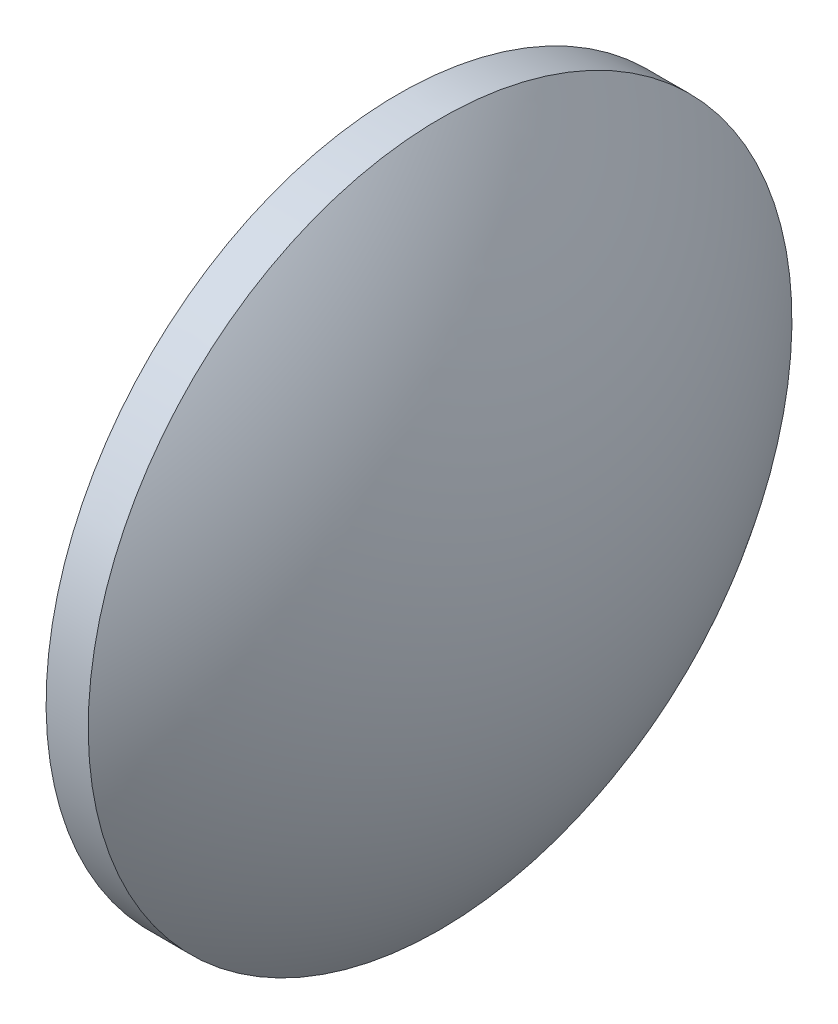
SolidWorks part; units mm, degrees
ref_plane "前视基准面" through (0, 0, 0) normal (0, 0, 1) x (1, 0, 0)
ref_plane "上视基准面" through (0, 0, 0) normal (0, 1, 0) x (1, 0, 0)
ref_plane "右视基准面" through (0, 0, 0) normal (1, 0, 0) x (0, 0, -1)
sketch "草图1" plane through (0, 0, 0) normal (0, 0, 1) x (1, 0, 0)
  line L0 (464.6857, 46.9494) -> (485.8127, 46.9084) construction
  line L1 (469.3335, 46.9404) -> (469.3335, 71.9404)
  line L2 (469.3335, 71.9404) -> (472.3335, 71.9404)
  line L3 (480.7635, 46.9182) -> (469.3335, 46.9404)
  arc A0 (480.7635, 46.9182) -> (472.3335, 71.9404) centre (439.4786, 46.9404) ccw
revolve "旋转1" add sketch "草图1" angle 360 about L0
